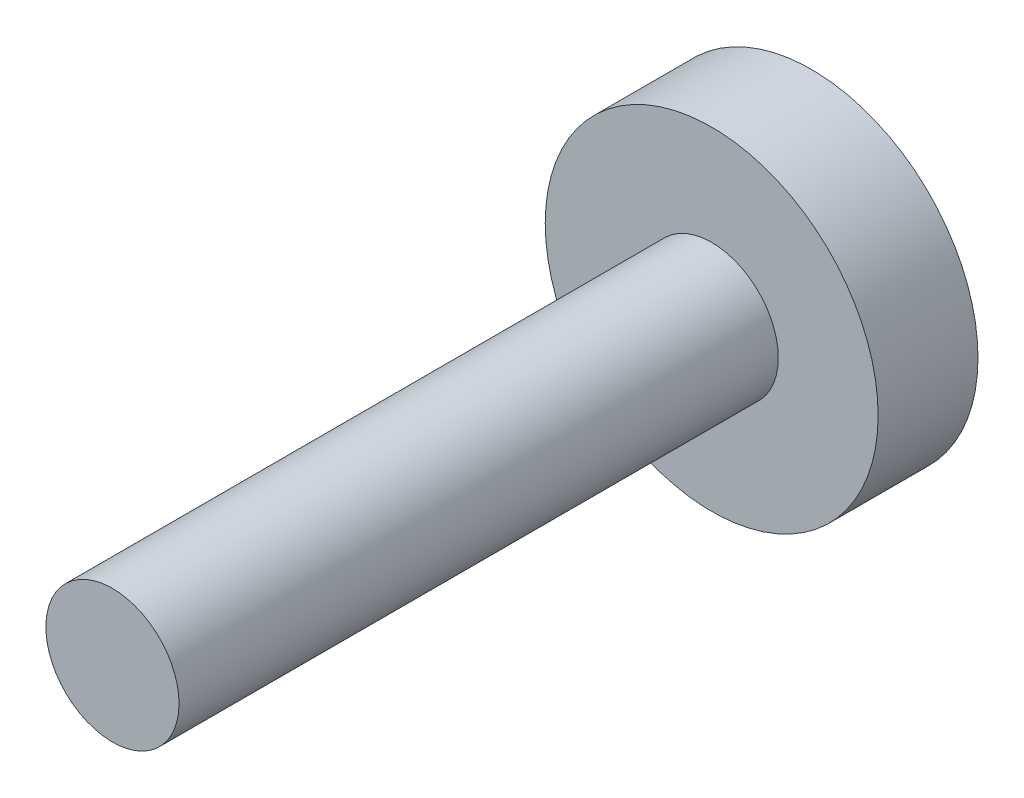
SolidWorks part; units mm, degrees
ref_plane "Front Plane" through (0, 0, 0) normal (0, 0, 1) x (1, 0, 0)
ref_plane "Top Plane" through (0, 0, 0) normal (0, 1, 0) x (1, 0, 0)
ref_plane "Right Plane" through (0, 0, 0) normal (1, 0, 0) x (0, 0, -1)
sketch "Sketch1" plane through (0, 0, 0) normal (0, 0, 1) x (1, 0, 0)
  circle A0 centre (0, 0) radius 5
extrude "Boss-Extrude1" add sketch "Sketch1" along normal blind 3
sketch "Sketch2" plane through (0, 0, 3) normal (0, 0, 1) x (1, 0, 0)
  circle A0 centre (0, 0) radius 2
extrude "Boss-Extrude2" add sketch "Sketch2" along normal blind 18
